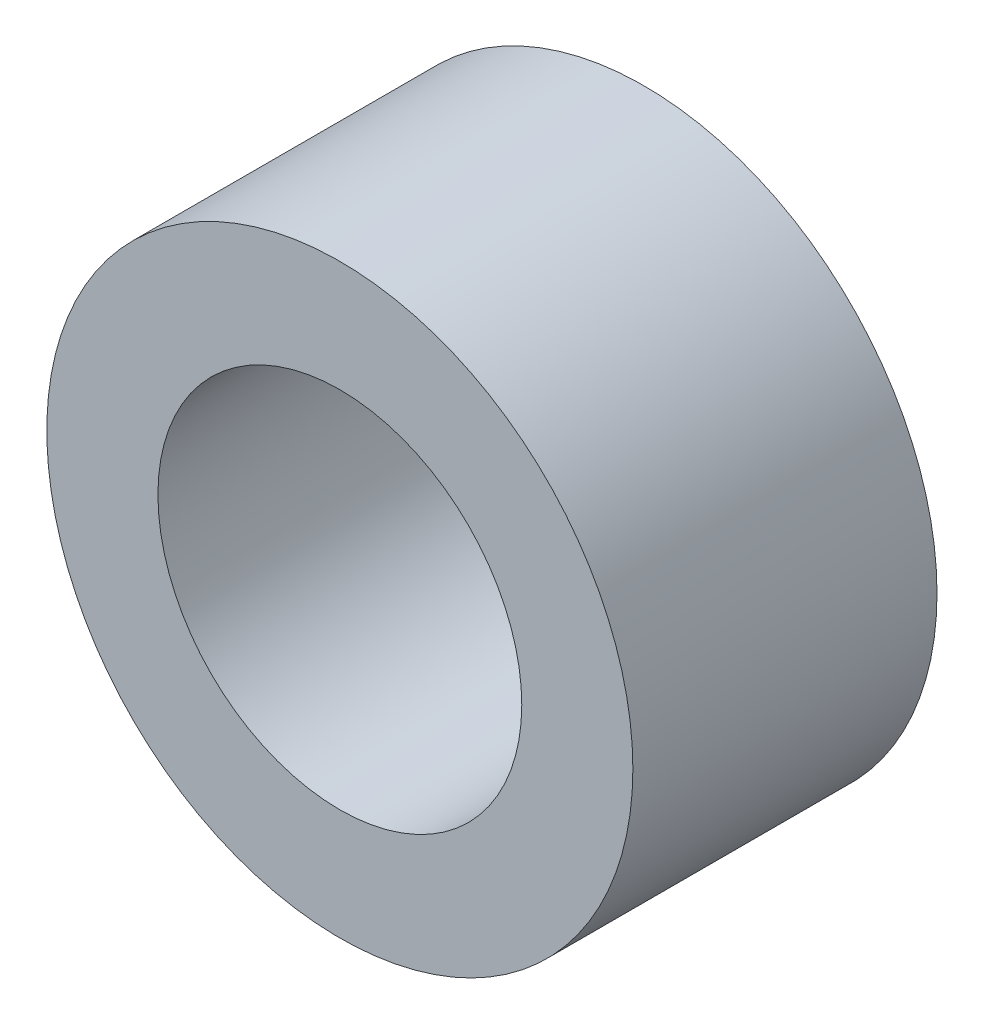
SolidWorks part; units mm, degrees
ref_plane "Front Plane" through (0, 0, 0) normal (0, 0, 1) x (1, 0, 0)
ref_plane "Top Plane" through (0, 0, 0) normal (0, 1, 0) x (1, 0, 0)
ref_plane "Right Plane" through (0, 0, 0) normal (1, 0, 0) x (0, 0, -1)
ref_plane "Plane1" through (0, 320.5214, 0) normal (0, 1, 0) x (1, 0, 0)
sketch "Sketch1" plane through (0, 320.5214, 0) normal (0, 1, 0) x (1, 0, 0)
  line L0 (5.3594, 0) -> (5.3594, 5.5626)
  line L1 (5.3594, 5.5626) -> (3.3274, 5.5626)
  line L2 (3.3274, 5.5626) -> (3.3274, 0)
  line L3 (3.3274, 0) -> (5.3594, 0)
  line L4 (0, 5.5626) -> (0, 0) construction
  point P6 (135.2684, -6.0047)
  point P7 (38.4099, -2.5927)
  point P8 (0, 0)
  dimension "D1" = 3.3274
  dimension "D2" = 5.3594
  dimension "D3" = 5.5626
revolve "Revolve1" add sketch "Sketch1" angle 360 about L4
